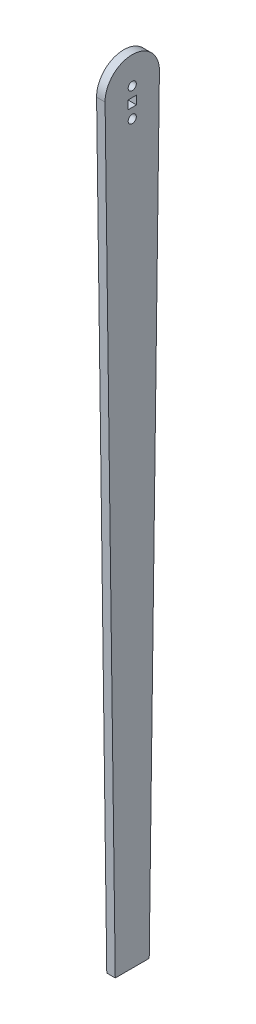
SolidWorks part; units mm, degrees
ref_plane "Front Plane" through (0, 0, 0) normal (0, 0, 1) x (1, 0, 0)
ref_plane "Top Plane" through (0, 0, 0) normal (0, 1, 0) x (1, 0, 0)
ref_plane "Right Plane" through (0, 0, 0) normal (1, 0, 0) x (0, 0, -1)
sketch "Sketch1" plane through (0, 0, 0) normal (1, 0, 0) x (0, 0, -1)
  line L0 (-6.35, -285.75) -> (6.35, -285.75)
  line L1 (-6.35, -285.75) -> (-10.1591, -0.1355)
  line L2 (0, -1000) -> (0, 49000) construction
  line L3 (6.35, -285.75) -> (10.1591, -0.1355)
  line L5 (-1.5875, -3.7465) -> (1.5875, -3.7465)
  line L6 (-1.5875, -3.7465) -> (-1.5875, -6.9215)
  line L7 (-1.5875, -6.9215) -> (1.5875, -6.9215)
  line L8 (1.5875, -3.7465) -> (1.5875, -6.9215)
  arc A0 (-10.1591, -0.1355) -> (10.1591, -0.1355) centre (0, 0) cw
  circle A1 centre (0, 0) radius 1.524
  circle A2 centre (0, -10.668) radius 1.524
  point P8 (0, -285.75)
  dimension "D1" = 285.75
  dimension "D2" = 10.16
  dimension "D4" = 3.048
  dimension "D3" = 12.7
  dimension "D5" = 3.175
  dimension "D6" = 10.668
  dimension "D7" = 3.175
  dimension "D8" = 3.7465
  dimension "D9" = 1.5875
extrude "Boss-Extrude1" add sketch "Sketch1" along normal blind 3.175
